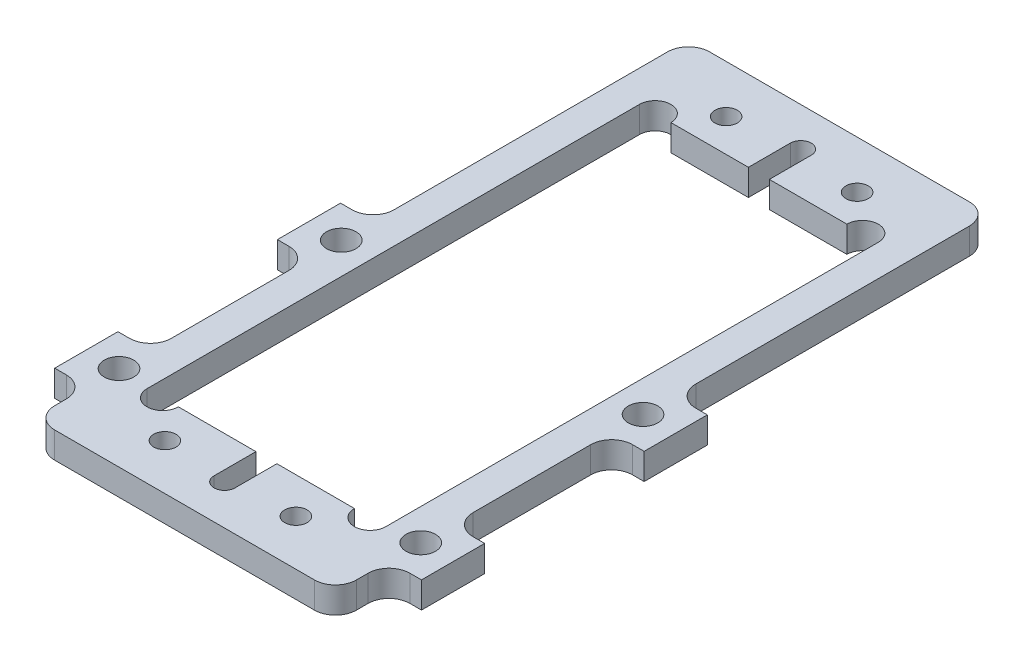
SolidWorks part; units mm, degrees
material "6061 Alloy"
ref_plane "Front Plane" through (0, 0, 0) normal (0, 0, 1) x (1, 0, 0)
ref_plane "Top Plane" through (0, 0, 0) normal (0, 1, 0) x (1, 0, 0)
ref_plane "Right Plane" through (0, 0, 0) normal (1, 0, 0) x (0, 0, -1)
sketch "Sketch1" plane through (0, 0, 0) normal (0, 1, 0) x (1, 0, 0)
  line L0 (18.288, -9.6647) -> (22.225, -9.6647)
  line L1 (-18.288, -23.8125) -> (18.288, -23.8125)
  line L2 (-18.288, -23.8125) -> (-18.288, -17.3228)
  line L3 (-18.288, 55.5625) -> (18.288, 55.5625)
  line L4 (18.288, -23.8125) -> (18.288, -17.3228)
  line L5 (-22.225, -17.3228) -> (-18.288, -17.3228)
  line L6 (-22.225, -17.3228) -> (-22.225, -9.6647)
  line L7 (-22.225, 17.3228) -> (-18.288, 17.3228)
  line L8 (22.225, -17.3228) -> (22.225, -9.6647)
  line L9 (0, 0) -> (-31.7584, 0) construction
  line L10 (-31.7584, 0) -> (-18.288, -13.4704) construction
  line L11 (-22.225, -9.6647) -> (-18.288, -9.6647)
  line L12 (-18.288, 17.3228) -> (-18.288, 55.5625)
  line L13 (-22.225, 9.6647) -> (-18.288, 9.6647)
  line L14 (-18.288, -9.6647) -> (-18.288, 9.6647)
  line L15 (18.288, 9.6647) -> (22.225, 9.6647)
  line L17 (18.288, -9.6647) -> (18.288, 9.6647)
  line L18 (22.225, 9.6647) -> (22.225, 17.3228)
  line L19 (-22.225, 9.6647) -> (-22.225, 17.3228)
  line L20 (-18.288, -9.6647) -> (-18.288, 9.6647)
  line L21 (18.288, -9.6647) -> (18.288, 9.6647)
  line L22 (18.288, 17.3228) -> (18.288, 55.5625)
  line L23 (18.288, 17.3228) -> (22.225, 17.3228)
  line L24 (18.288, -17.3228) -> (22.225, -17.3228)
  line L25 (-31.7584, 0) -> (-18.288, 13.4704) construction
  line L26 (0, -23.8125) -> (0, 0) construction
  line L28 (-14.478, -13.8906) -> (14.478, -13.8906)
  line L29 (-14.478, -13.8906) -> (-14.478, 45.7994)
  line L30 (-14.478, 45.7994) -> (14.478, 45.7994)
  line L31 (14.478, -13.8906) -> (14.478, 45.7994)
  point P4 (-7.9375, -18.2562)
  point P6 (0, 0)
  point P9 (7.9375, -18.2562)
  point P10 (-7.9375, 49.7649)
  point P11 (7.9375, 49.7649)
  point P31 (18.288, -13.4704)
  point P32 (18.288, 13.4704)
  dimension "D1" = 36.576
  dimension "D2" = 79.375
  dimension "D3" = 18.288
  dimension "D4" = 23.8125
  dimension "D5" = 18.2562
  dimension "D6" = 7.9375
  dimension "D9" = 5.5563
  dimension "D10" = 34.6456
  dimension "D11" = 44.45
  dimension "D12" = 19.3294
  dimension "D13" = 9.6647
  dimension "D14" = 19.05
  dimension "D15" = 19.05
  dimension "D16" = 90
  dimension "D17" = 28.956
  dimension "D18" = 14.478
  dimension "D19" = 59.69
  dimension "D20" = 13.8906
  dimension "D7" = 2
  dimension "D8" = 2
extrude "Boss-Extrude1" add sketch "Sketch1" along normal blind 3.175 contours L4 L24 L8 L0 L17 L15 L18 L23 L22 L3 L12 L7 L19 L13 L14 L11 L6 L5 L2 L1 L31 L28 L29 L30
hole_wizard "#6-32 Tapped Hole1" positions "Sketch3" profile "Sketch2" tap size "#6-32" standard "Ansi Inch" end condition up to next
sketch "Sketch3" plane through (0, 0, 0) normal (0, -1, 0) x (1, 0, 0)
  point P0 (-7.9375, 18.2562)
  point P1 (7.9375, 18.2562)
  point P4 (7.9375, -49.7649)
  point P7 (-7.9375, -49.7649)
sketch "Sketch2" plane through (-7.9375, 0, 18.2562) normal (1, 0, 0) x (0, 0, -1)
  line L0 (0, 0) -> (0, 3.175)
  line L1 (0, 3.175) -> (1.3525, 3.175)
  line L2 (1.3525, 3.175) -> (1.3525, 0)
  line L5 (1.3525, 0) -> (0, 0)
  line L11 (0, -6.35) -> (0, 107.95) construction
  dimension "Thread Major Dia." = 2.7051
  dimension "Thru Tap Drill Depth" = 3.175
hole_wizard "9/64 (0.14063) Diameter Hole1" positions "Sketch5" profile "Sketch6" hole size "9/64" standard "Ansi Inch" end condition up to next
sketch "Sketch5" plane through (0, 0, 0) normal (0, -1, 0) x (1, 0, 0)
  point P4 (18.288, -13.4704)
  point P7 (18.288, 13.4704)
  point P35 (-18.288, -13.4704)
  point P37 (-18.288, 13.4704)
sketch "Sketch6" plane through (18.288, 0, -13.4704) normal (1, 0, 0) x (0, 0, -1)
  line L0 (0, 0) -> (0, 3.175)
  line L1 (0, 3.175) -> (1.786, 3.175)
  line L2 (1.786, 3.175) -> (1.786, 0)
  line L5 (1.786, 0) -> (0, 0)
  line L11 (0, -6.35) -> (0, 107.95) construction
  dimension "Thru Hole Dia." = 3.572
  dimension "Thru Hole Depth" = 3.175
fillet "Fillet1" radius 2.54 12 edges at (18.288, 1.5875, 23.8125) (18.288, 1.5875, 17.3228) (18.288, 1.5875, 9.6647) (18.288, 1.5875, -9.6647) (18.288, 1.5875, -17.3228) (18.288, 1.5875, -55.5625) (-18.288, 1.5875, -55.5625) (-18.288, 1.5875, -17.3228) (-18.288, 1.5875, -9.6647) (-18.288, 1.5875, 9.6647) (-18.288, 1.5875, 17.3228) (-18.288, 1.5875, 23.8125)
sketch "Sketch7" plane through (0, 3.175, 0) normal (0, 1, 0) x (1, 0, 0)
  line L0 (0, -13.8906) -> (0, -18.9706) construction
  line L1 (-14.478, -13.8906) -> (14.478, -13.8906) construction
  line L2 (1.27, -13.8906) -> (1.27, -18.9706)
  line L3 (-1.27, -13.8906) -> (-1.27, -18.9706)
  line L4 (0, 45.7994) -> (0, 50.8794) construction
  line L5 (-14.478, 45.7994) -> (14.478, 45.7994) construction
  line L6 (-1.27, 45.7994) -> (-1.27, 50.8794)
  line L7 (1.27, 45.7994) -> (1.27, 50.8794)
  arc A0 (1.27, -13.8906) -> (-1.27, -13.8906) centre (0, -13.8906) ccw
  arc A1 (-1.27, -18.9706) -> (1.27, -18.9706) centre (0, -18.9706) ccw
  arc A2 (-1.27, 45.7994) -> (1.27, 45.7994) centre (0, 45.7994) ccw
  arc A3 (1.27, 50.8794) -> (-1.27, 50.8794) centre (0, 50.8794) ccw
  point P5 (0, -16.4306)
  point P14 (0, 48.3394)
  dimension "D1" = 5.08
  dimension "D2" = 2.54
  dimension "D3" = 5.08
  dimension "D4" = 2.54
extrude "Cut-Extrude1" cut sketch "Sketch7" against normal up to next
sketch "Sketch8" plane through (0, 3.175, 0) normal (0, 1, 0) x (1, 0, 0)
  line L0 (-14.478, 45.7994) -> (-1.27, 45.7994) construction
  line L1 (-14.478, 15.9544) -> (14.478, 15.9544) construction
  line L2 (-14.478, -13.8906) -> (-14.478, 45.7994) construction
  line L3 (14.478, -13.8906) -> (14.478, 45.7994) construction
  line L4 (0, 15.9544) -> (0, -20.2406) construction
  line L5 (14.478, 45.7994) -> (10.668, 45.7994)
  line L6 (-14.478, 45.7994) -> (-10.668, 45.7994)
  line L7 (-14.478, -13.8906) -> (-10.668, -13.8906)
  line L8 (10.668, -13.8906) -> (14.478, -13.8906)
  arc A0 (-14.478, 45.7994) -> (-10.668, 45.7994) centre (-12.573, 45.7994) cw
  arc A1 (-14.478, -13.8906) -> (-10.668, -13.8906) centre (-12.573, -13.8906) ccw
  arc A2 (-1.27, -18.9706) -> (1.27, -18.9706) centre (0, -18.9706) ccw construction
  arc A3 (14.478, -13.8906) -> (10.668, -13.8906) centre (12.573, -13.8906) cw
  arc A4 (14.478, 45.7994) -> (10.668, 45.7994) centre (12.573, 45.7994) ccw
  dimension "D1" = 1.905
extrude "Cut-Extrude2" cut sketch "Sketch8" against normal up to next
